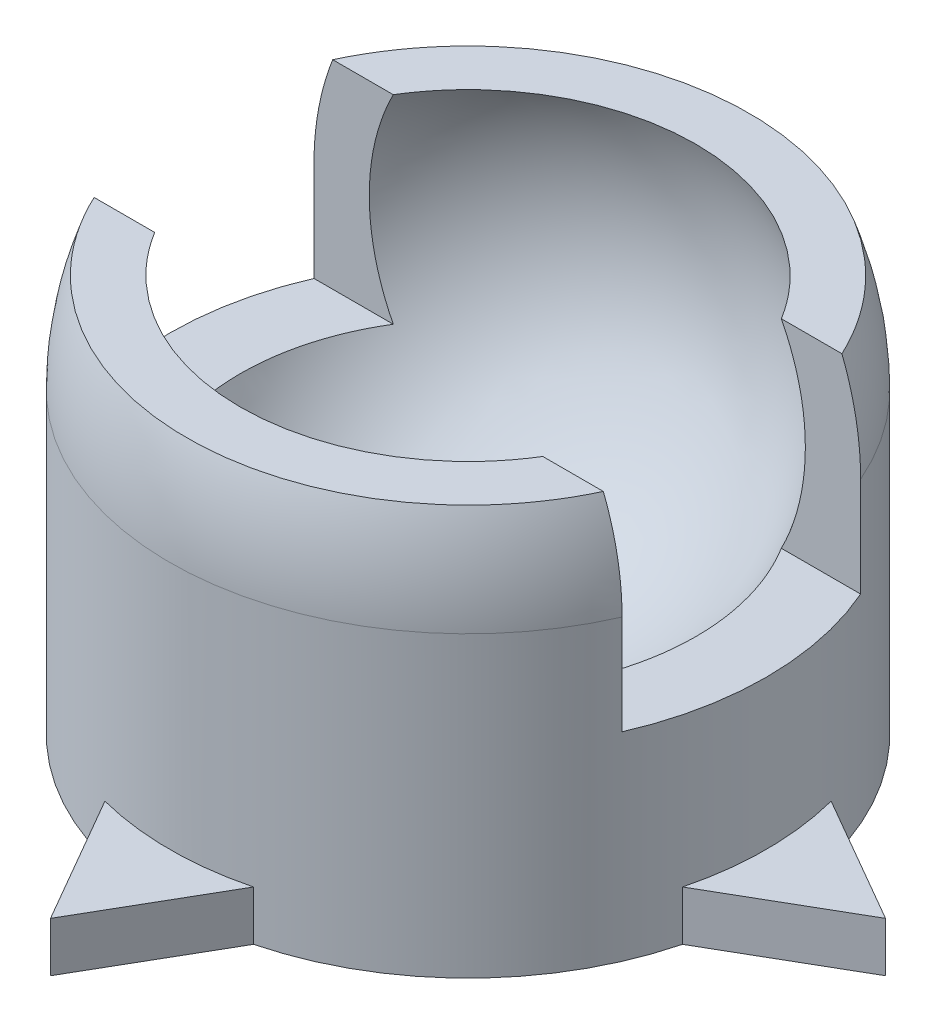
SolidWorks part; units mm, degrees
ref_plane "Front Plane" through (0, 0, 0) normal (0, 0, 1) x (1, 0, 0)
ref_plane "Top Plane" through (0, 0, 0) normal (0, 1, 0) x (1, 0, 0)
ref_plane "Right Plane" through (0, 0, 0) normal (1, 0, 0) x (0, 0, -1)
sketch "Sketch7" plane through (0, 0, 0) normal (0, 1, 0) x (1, 0, 0)
  line L0 (-8.6029, 0) -> (8.917, 0) construction
  line L1 (-6.25, 0) -> (6.25, 0) construction
  line L3 (-7.3951, 1.25) -> (7.3951, 1.25) construction
  line L4 (7.5, 0) -> (6.25, 0)
  line L5 (-6.25, 0) -> (-7.5, 0)
  arc A0 (-6.25, 0) -> (6.25, 0) centre (0, 0) ccw
  arc A1 (-7.5, 0) -> (7.5, 0) centre (0, 0) ccw
  arc A3 (-7.3951, 1.25) -> (7.3951, 1.25) centre (0, 0) ccw construction
  dimension "D1" = 6.25
  dimension "D2" = 1.25
revolve "Revolve1" add sketch "Sketch7" angle 360 about L5
sketch "Sketch9" plane through (0, 0, 0) normal (0, 1, 0) x (1, 0, 0)
  circle A0 centre (0, 0) radius 7.5
  circle A1 centre (0, 0) radius 7.5
extrude "Boss-Extrude2" add sketch "Sketch9" against normal blind 7.5 separate body
ref_plane "Plane4" through (0, 2.5, 0) normal (0, -1, 0) x (-1, 0, 0)
sketch "Sketch10" plane through (0, 2.5, 0) normal (0, -1, 0) x (-1, 0, 0)
  line L1 (-9.2945, 8.6588) -> (8.594, 8.6588)
  line L2 (-9.2945, 8.6588) -> (-9.2945, -9.8653)
  line L3 (-9.2945, -9.8653) -> (8.594, -9.8653)
  line L4 (8.594, 8.6588) -> (8.594, -9.8653)
extrude "Cut-Extrude2" cut sketch "Sketch10" against normal blind 20
sketch "Sketch12" plane through (0, 0, 0) normal (0, 1, 0) x (1, 0, 0)
  line L0 (-8.9603, 0) -> (9.1979, 0) construction
  line L1 (-6.75, 0) -> (6.75, 0)
  arc A0 (-6.75, 0) -> (6.75, 0) centre (0, 0) cw
  dimension "D1" = 6.75
revolve "Cut-Revolve4" cut sketch "Sketch12" angle 360 about L0
ref_plane "Plane5" through (7.5, 0, 0) normal (1, 0, 0) x (0, 0, -1)
sketch "Sketch15" plane through (7.5, 0, 0) normal (1, 0, 0) x (0, 0, -1)
  line L0 (0, 0) -> (0, -2.5) construction
  line L1 (0, 0) -> (3.0679, 0) construction
  line L2 (7.5, 0) -> (-7.5, 0) construction
  line L3 (0, 0) -> (0, 2.5) construction
  line L4 (7.0711, 2.5) -> (-7.0711, 2.5) construction
  line L5 (-3, -2.5) -> (3, -2.5)
  line L6 (-3, 2.5) -> (3, 2.5)
  line L7 (5.7282, 2.5) -> (-5.7282, 2.5) construction
  line L8 (-3, 2.5) -> (-3, -2.5)
  line L9 (3, -2.5) -> (3, 2.5)
  point P12 (0, -2.5)
  point P18 (0, 2.5)
  dimension "D1" = 2.5
  dimension "D2" = 6
  dimension "D3" = 6
extrude "Cut-Extrude3" cut sketch "Sketch15" against normal blind 20
sketch "Sketch18" plane through (0, -7.5, 0) normal (0, -1, 0) x (1, 0, 0)
  line L1 (-11.8358, 8.6097) -> (12.2835, 8.6097)
  line L2 (-11.8358, 8.6097) -> (-11.8358, -9.783)
  line L3 (-11.8358, -9.783) -> (12.2835, -9.783)
  line L4 (12.2835, 8.6097) -> (12.2835, -9.783)
sketch "Sketch19" plane through (0, -7.5, 0) normal (0, -1, 0) x (1, 0, 0)
  circle A0 centre (0, 0) radius 8.5
sketch "Sketch20" plane through (0, -7.5, 0) normal (0, -1, 0) x (1, 0, 0)
sketch "Sketch22" plane through (0, -7.5, 0) normal (0, -1, 0) x (1, 0, 0)
  line L1 (-10.2554, 0) -> (-7.4285, 1.0335)
  line L2 (-10.2554, 0) -> (-7.4314, -1.0122)
  circle A0 centre (0, 0) radius 7.5 construction
  circle A2 centre (0, 0) radius 7.5
  arc A3 (-7.4285, 1.0335) -> (-7.4314, -1.0122) centre (0, 0) ccw
  dimension "D1" = 0
sketch "Sketch23" plane through (0, -7.5, 0) normal (0, -1, 0) x (1, 0, 0)
  line L1 (-10.5, 0) -> (-7.2635, -1.8686)
  line L2 (-10.5, 0) -> (-7.2635, 1.8686)
  circle A0 centre (0, 0) radius 7.5 construction
  circle A2 centre (0, 0) radius 7.5
  arc A3 (-7.2635, 1.8686) -> (-7.2635, -1.8686) centre (0, 0) ccw
  point P0 (0, 0)
  dimension "D1" = 0
extrude "Boss-Extrude4" add sketch "Sketch23" against normal blind 1.25
mirror "Mirror1" about plane through (0, 0, 0) normal (1, 0, 0) of "Boss-Extrude4"
sketch "Sketch24" plane through (0, -7.5, 0) normal (0, -1, 0) x (1, 0, 0)
  circle A0 centre (0, 0) radius 1.5
extrude "Cut-Extrude4" cut sketch "Sketch24" against normal blind 15
sketch "Sketch25" plane through (0, -7.5, 0) normal (0, -1, 0) x (1, 0, 0)
  line L1 (0, 10.5) -> (1.8686, 7.2635)
  line L2 (0, 10.5) -> (-1.8686, 7.2635)
  line L6 (-7.2635, 1.8686) -> (-10.5, 0)
  line L7 (-10.5, 0) -> (-7.2635, -1.8686)
  line L8 (7.2635, -1.8686) -> (10.5, 0)
  line L9 (10.5, 0) -> (7.2635, 1.8686)
  arc A0 (7.2635, 1.8686) -> (-7.2635, 1.8686) centre (0, 0) ccw construction
  arc A3 (7.2635, 1.8686) -> (-7.2635, 1.8686) centre (0, 0) ccw
  arc A4 (-7.2635, -1.8686) -> (7.2635, -1.8686) centre (0, 0) ccw
  arc A5 (1.8686, 7.2635) -> (-1.8686, 7.2635) centre (0, 0) ccw
  dimension "D1" = 0
extrude "Boss-Extrude5" add sketch "Sketch25" against normal blind 1.25
mirror "Mirror2" about plane through (0, 0, 0) normal (0, 0, 1) of "Boss-Extrude5"
